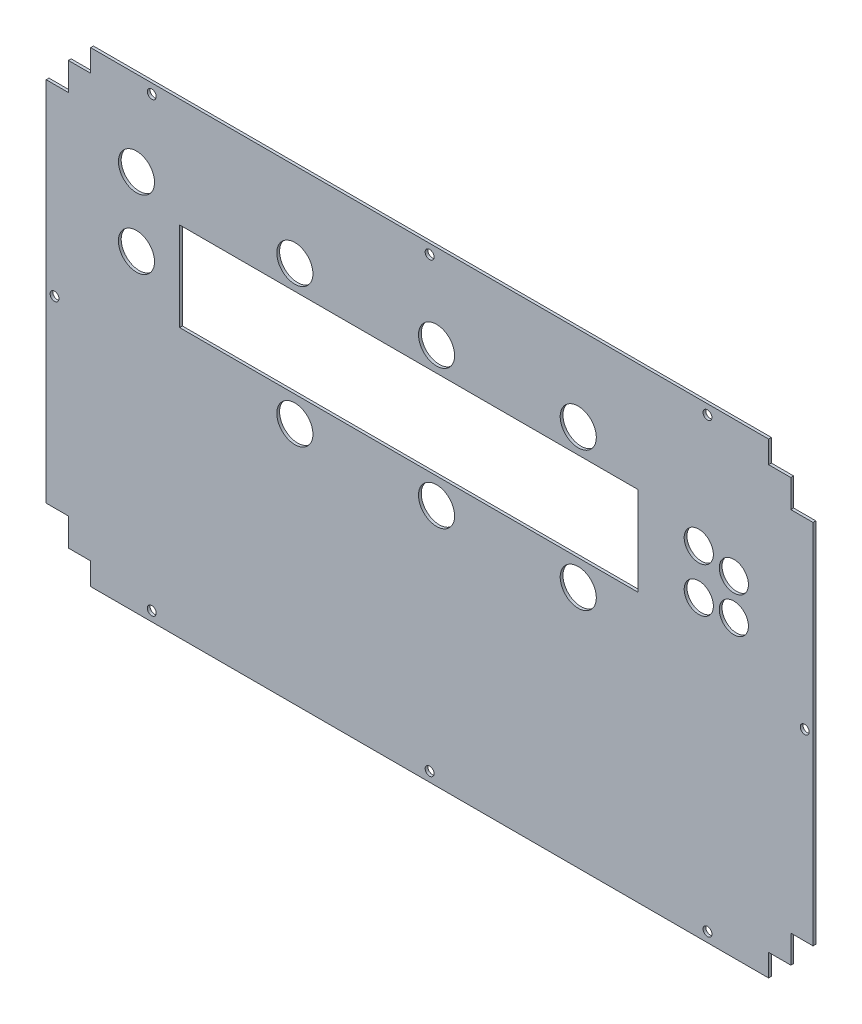
SolidWorks part; units mm, degrees
material "7079 Alloy"
ref_plane "Front" through (0, 0, 0) normal (0, 0, 1) x (1, 0, 0)
ref_plane "Top" through (0, 0, 0) normal (0, 1, 0) x (1, 0, 0)
ref_plane "Right" through (0, 0, 0) normal (1, 0, 0) x (0, 0, -1)
sketch "Sketch1" plane through (0, 0, 0) normal (0, 0, 1) x (1, 0, 0)
  line L0 (142, -87) -> (-142, 87) construction
  line L1 (-122, 84) -> (122, 84)
  line L2 (-138, -66) -> (-138, 66)
  line L3 (-122, -84) -> (122, -84)
  line L4 (138, 66) -> (138, -66)
  line L5 (122, 84) -> (122, 76)
  line L6 (122, 76) -> (130, 76)
  line L7 (130, 76) -> (130, 66)
  line L8 (130, 66) -> (138, 66)
  line L9 (0, 48.7465) -> (0, -33.5112) construction
  line L10 (-62.6461, 0) -> (60.1053, 0) construction
  line L11 (130, -66) -> (138, -66)
  line L12 (130, -76) -> (130, -66)
  line L13 (122, -76) -> (130, -76)
  line L14 (122, -84) -> (122, -76)
  line L15 (-122, -84) -> (-122, -76)
  line L16 (-130, -76) -> (-122, -76)
  line L17 (-130, -76) -> (-130, -66)
  line L18 (-138, -66) -> (-130, -66)
  line L19 (-138, 66) -> (-130, 66)
  line L20 (-130, 76) -> (-130, 66)
  line L21 (-130, 76) -> (-122, 76)
  line L22 (-122, 84) -> (-122, 76)
  dimension "D1" = 244
  dimension "D2" = 132
  dimension "D3" = 8
  dimension "D4" = 8
  dimension "D5" = 16
  dimension "D6" = 10
extrude "Extrude1" add sketch "Sketch1" along normal blind 1
sketch "Sketch2" plane through (0, 0, 1) normal (0, 0, 1) x (1, 0, 0)
  line L0 (122, 84) -> (-122, 84) construction
  line L1 (-90, 44.75) -> (75, 44.75)
  line L2 (-90, 44.75) -> (-90, 12.75)
  line L3 (-90, 12.75) -> (75, 12.75)
  line L4 (75, 44.75) -> (75, 12.75)
  line L5 (138, -66) -> (138, 66) construction
  dimension "D1" = 32
  dimension "D2" = 165
  dimension "D3" = 39.25
  dimension "D4" = 63
extrude "Cut-Extrude1" cut sketch "Sketch2" against normal blind 1
sketch "Sketch3" plane through (0, 0, 1) normal (0, 0, 1) x (1, 0, 0)
  line L0 (122, 84) -> (-122, 84) construction
  line L1 (-138, 66) -> (-138, -66) construction
  line L2 (138, -66) -> (138, 66) construction
  circle A0 centre (-105.5, 53.5) radius 6.5
  circle A1 centre (-105.5, 28.75) radius 6.5
  circle A2 centre (-48.5, 3.5) radius 6.5
  circle A3 centre (2.5, 3.5) radius 6.5
  circle A4 centre (53.5, 3.5) radius 6.5
  circle A5 centre (53.5, 53.5) radius 6.5
  circle A6 centre (2.5, 53.5) radius 6.5
  circle A7 centre (-48.5, 53.5) radius 6.5
  circle A8 centre (96.8733, 38.0928) radius 5.25
  circle A9 centre (109.5, 35) radius 5.25
  circle A10 centre (109.5, 22) radius 5.25
  circle A11 centre (96.8733, 22) radius 5.25
  dimension "D1" = 13
  dimension "D2" = 30.5
  dimension "D3" = 24.75
  dimension "D5" = 80.5
  dimension "D6" = 57
  dimension "D7" = 51
  dimension "D8" = 51
  dimension "D9" = 10.5
  dimension "D10" = 13
  dimension "D11" = 28.5
  dimension "D12" = 49
  dimension "D13" = 13
  dimension "D4" = 32.5
extrude "Cut-Extrude2" cut sketch "Sketch3" against normal blind 1
sketch "Esboço1" plane through (0, 0, 1) normal (0, 0, 1) x (1, 0, 0)
  line L2 (-152.406, 0) -> (152.406, 0) construction
  circle A0 centre (0, -80.5) radius 1.6
  circle A1 centre (-100, -80.5) radius 1.6
  circle A2 centre (100, -80.5) radius 1.6
  circle A3 centre (-135, 0) radius 1.6
  circle A4 centre (135, 0) radius 1.6
  circle A6 centre (100, 80.5) radius 1.6
  circle A7 centre (-100, 80.5) radius 1.6
  circle A8 centre (0, 80.5) radius 1.6
  dimension "D1" = 100
  dimension "D2" = 100
  dimension "D3" = 3.2
  dimension "D4" = 3.2
  dimension "D5" = 3.2
  dimension "D6" = 270
  dimension "D7" = 135
  dimension "D8" = 3.2
  dimension "D9" = 3.2
  dimension "D12" = 161
extrude "Corte-extrusão1" cut sketch "Esboço1" against normal through all
